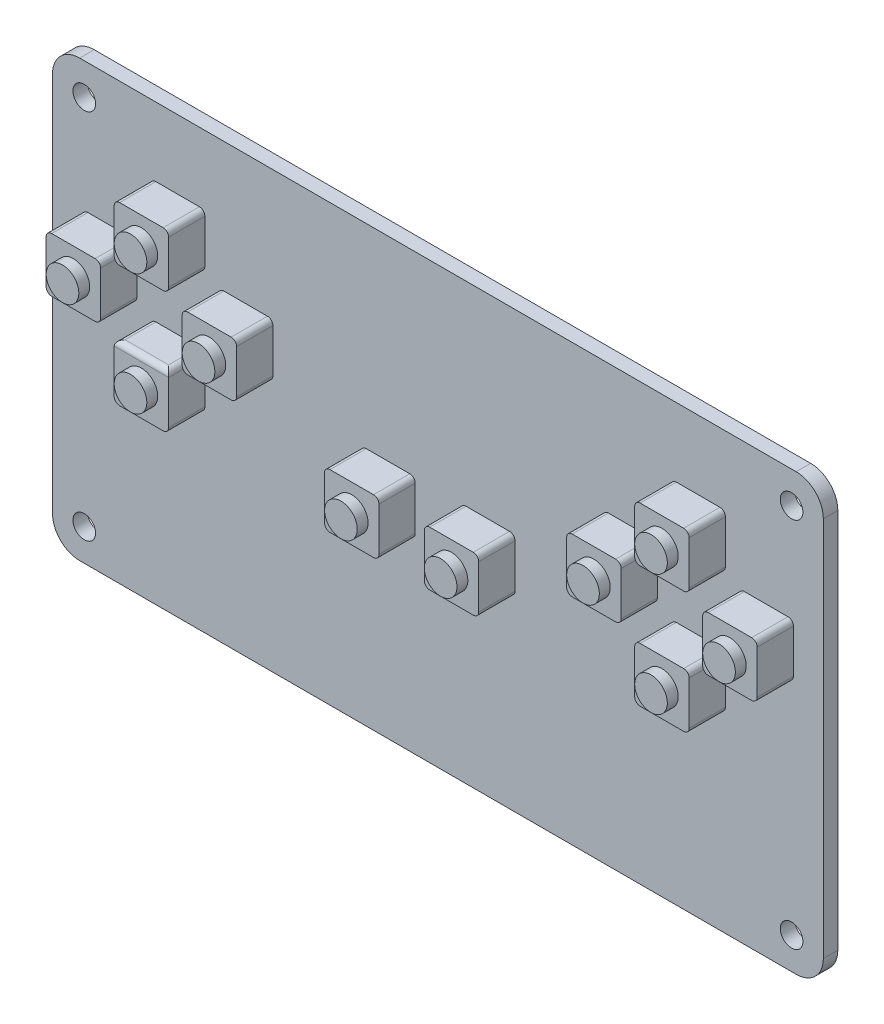
SolidWorks part; units mm, degrees
ref_plane "前视基准面" through (0, 0, 0) normal (0, 0, 1) x (1, 0, 0)
ref_plane "上视基准面" through (0, 0, 0) normal (0, 1, 0) x (1, 0, 0)
ref_plane "右视基准面" through (0, 0, 0) normal (1, 0, 0) x (0, 0, -1)
sketch "Sketch1" plane through (0, 0, 0) normal (0, 0, 1) x (1, 0, 0)
  line L1 (42.5, -24) -> (-42.5, -24)
  line L2 (42.5, -24) -> (42.5, 24)
  line L3 (42.5, 24) -> (-42.5, 24)
  line L4 (-42.5, -24) -> (-42.5, 24)
  line L5 (42.5, -24) -> (-42.5, 24) construction
  line L6 (42.5, 24) -> (-42.5, -24) construction
  point P0 (0, 0)
  dimension "D1" = 48
  dimension "D2" = 85
extrude "Boss-Extrude1" add sketch "Sketch1" along normal blind 1.6
sketch "Sketch2" plane through (0, 0, 1.6) normal (0, 0, 1) x (1, 0, 0)
  line L1 (39, 20.5) -> (-39, 20.5) construction
  line L2 (39, 20.5) -> (39, -20.5) construction
  line L3 (39, -20.5) -> (-39, -20.5) construction
  line L4 (-39, 20.5) -> (-39, -20.5) construction
  line L5 (39, 20.5) -> (-39, -20.5) construction
  line L6 (39, -20.5) -> (-39, 20.5) construction
  circle A0 centre (-39, 20.5) radius 1.25
  circle A1 centre (39, 20.5) radius 1.25
  circle A2 centre (39, -20.5) radius 1.25
  circle A3 centre (-39, -20.5) radius 1.25
  point P0 (0, 0)
  dimension "D3" = 2.5
  dimension "D4" = 2
  dimension "D1" = 78
  dimension "D2" = 41
  dimension "D5" = 2
extrude "Cut-Extrude1" cut sketch "Sketch2" against normal blind 5
fillet "Fillet1" radius 3 4 edges at (-42.5, -24, 0.8) (42.5, -24, 0.8) (42.5, 24, 0.8) (-42.5, 24, 0.8)
sketch "草图1" plane through (0, 0, 1.6) normal (0, 0, 1) x (1, 0, 0)
  line L0 (39.5, 24) -> (-39.5, 24) construction
  line L1 (-31.7, 16.4) -> (-25.7, 16.4)
  line L2 (-31.7, 16.4) -> (-31.7, 10.4)
  line L3 (-31.7, 10.4) -> (-25.7, 10.4)
  line L4 (-25.7, 16.4) -> (-25.7, 10.4)
  line L5 (-28.7, 10.4) -> (-28.7, 3) construction
  line L6 (-42.5, 21) -> (-42.5, -21) construction
  line L7 (-39.5, -24) -> (39.5, -24) construction
  line L8 (-31.7, 3) -> (-25.7, 3)
  line L9 (-31.7, 3) -> (-31.7, -3)
  line L10 (-31.7, -3) -> (-25.7, -3)
  line L11 (-25.7, 3) -> (-25.7, -3)
  line L12 (-28.7, 6.7) -> (-2.636, 6.7) construction
  line L13 (-39.2, 9.7) -> (-33.2, 9.7)
  line L14 (-39.2, 9.7) -> (-39.2, 3.7)
  line L15 (-39.2, 3.7) -> (-33.2, 3.7)
  line L16 (-33.2, 9.7) -> (-33.2, 3.7)
  line L17 (-24.2, 9.7) -> (-18.2, 9.7)
  line L18 (-24.2, 9.7) -> (-24.2, 3.7)
  line L19 (-24.2, 3.7) -> (-18.2, 3.7)
  line L20 (-18.2, 9.7) -> (-18.2, 3.7)
  point P10 (-28.7, 16.4)
  point P15 (-28.7, 3)
  point P26 (-24.2, 6.7)
  point P27 (-33.2, 6.7)
  dimension "D1" = 6
  dimension "D2" = 6
  dimension "D3" = 7.6
  dimension "D4" = 13.8
  dimension "D5" = 6
  dimension "D6" = 6
  dimension "D7" = 21
  dimension "D8" = 3.3
  dimension "D9" = 6
  dimension "D10" = 6
  dimension "D11" = 6
  dimension "D12" = 6
  dimension "D13" = 21
extrude "凸台-拉伸1" add sketch "草图1" along normal blind 4
mirror "镜向1" about plane through (0, 0, 0) normal (1, 0, 0) of "凸台-拉伸1"
sketch "草图2" plane through (0, 0, 1.6) normal (0, 0, 1) x (1, 0, 0)
  line L0 (0, 24) -> (0, -24) construction
  line L1 (39.5, 24) -> (-39.5, 24) construction
  line L2 (-39.5, -24) -> (39.5, -24) construction
  line L4 (-8.5, 2.5) -> (-2.5, 2.5)
  line L5 (-8.5, 2.5) -> (-8.5, -3.5)
  line L6 (-8.5, -3.5) -> (-2.5, -3.5)
  line L7 (-2.5, 2.5) -> (-2.5, -3.5)
  line L8 (2.5, 2.5) -> (8.5, 2.5)
  line L9 (2.5, 2.5) -> (2.5, -3.5)
  line L10 (2.5, -3.5) -> (8.5, -3.5)
  line L11 (8.5, 2.5) -> (8.5, -3.5)
  dimension "D1" = 6
  dimension "D2" = 6
  dimension "D3" = 6
  dimension "D4" = 6
  dimension "D5" = 20.5
  dimension "D6" = 20.5
  dimension "D7" = 2.5
  dimension "D8" = 2.5
extrude "凸台-拉伸2" add sketch "草图2" along normal blind 4
sketch "草图3" plane through (0, 0, 5.6) normal (0, 0, 1) x (1, 0, 0)
  circle A0 centre (-36.2, 6.7) radius 1.8
  circle A1 centre (-28.7, 13.4) radius 1.8
  circle A2 centre (-21.2, 6.7) radius 1.8
  circle A3 centre (-28.7, 0) radius 1.8
  circle A4 centre (-5.5, -0.5) radius 1.8
  circle A5 centre (5.5, -0.5) radius 1.8
  circle A6 centre (21.2, 6.7) radius 1.8
  circle A7 centre (28.7, 0) radius 1.8
  circle A8 centre (36.2, 6.7) radius 1.8
  circle A9 centre (28.7, 13.4) radius 1.8
extrude "凸台-拉伸3" add sketch "草图3" along normal blind 1.2
fillet "圆角2" radius 0.6 41 edges at (25.7, 3, 3.6) (25.7, -3, 3.6) (31.7, -3, 3.6) (31.7, 3, 3.6) (39.2, 9.7, 3.6) (39.2, 3.7, 3.6) (33.2, 3.7, 3.6) (33.2, 9.7, 3.6) (31.7, 10.4, 3.6) (31.7, 16.4, 3.6) (25.7, 16.4, 3.6) (25.7, 10.4, 3.6) (18.2, 3.7, 3.6) (18.2, 9.7, 3.6) (24.2, 3.7, 3.6) (24.2, 9.7, 3.6) (8.5, 2.5, 3.6) (2.5, 2.5, 3.6) (2.5, -3.5, 3.6) (8.5, -3.5, 3.6) (-2.5, -3.5, 3.6) (-8.5, -3.5, 3.6) (-8.5, 2.5, 3.6) (-2.5, 2.5, 3.6) (-24.2, 9.7, 3.6) (-18.2, 3.7, 3.6) (-18.2, 9.7, 3.6) (-24.2, 3.7, 3.6) (-31.7, 3, 3.6) (-25.7, 3, 3.6) (-28.7, 3, 5.6) (-25.7, -3, 3.6) (-31.7, -3, 3.6) (-31.7, 16.4, 3.6) (-25.7, 16.4, 3.6) (-25.7, 10.4, 3.6) (-31.7, 10.4, 3.6) (-33.2, 9.7, 3.6) (-33.2, 3.7, 3.6) (-39.2, 3.7, 3.6) (-39.2, 9.7, 3.6)
